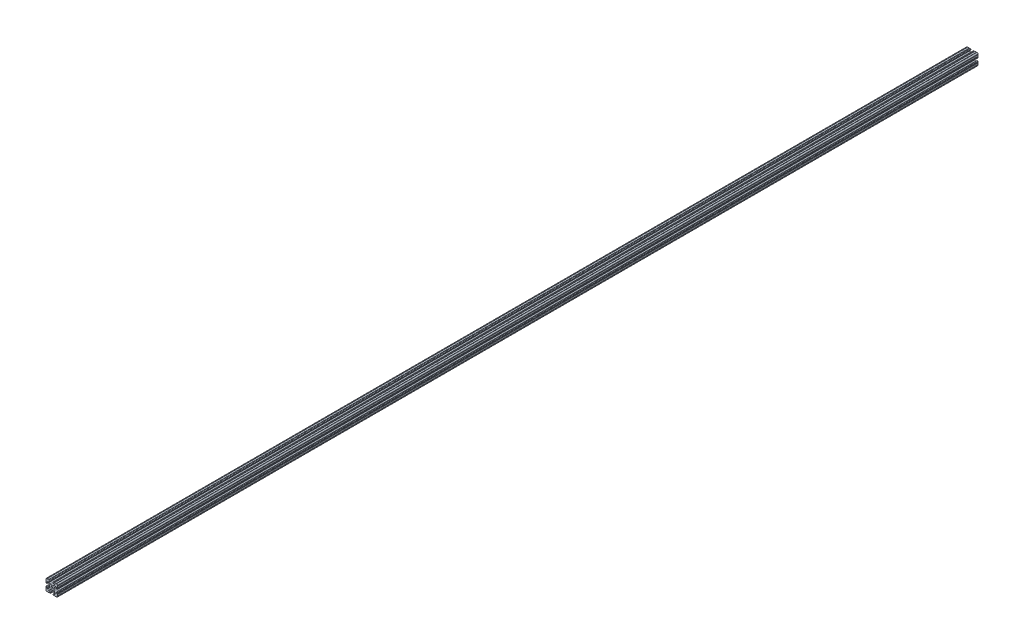
SolidWorks part; units mm, degrees
material "6061-T6 (SS)"
ref_plane "Front Plane" through (0, 0, 0) normal (0, 0, 1) x (1, 0, 0)
ref_plane "Top Plane" through (0, 0, 0) normal (0, 1, 0) x (1, 0, 0)
ref_plane "Right Plane" through (0, 0, 0) normal (1, 0, 0) x (0, 0, -1)
ref_plane "Plane1" through (0, 0, -304.8) normal (0, 0, -1) x (-1, 0, 0)
sketch "Sketch1" plane through (0, 0, -304.8) normal (0, 0, -1) x (-1, 0, 0)
  line L0 (14.3277, 19.05) -> (9.4982, 19.05)
  line L1 (7.9742, 19.05) -> (5.6176, 19.05)
  line L2 (4.064, 17.4964) -> (4.064, 16.5396)
  line L3 (5.6176, 14.986) -> (9.3853, 14.986)
  line L4 (10.287, 14.0843) -> (10.287, 13.5524)
  line L5 (10.0229, 12.9148) -> (5.2522, 8.144)
  line L6 (1.9022, 6.7564) -> (-1.9022, 6.7564)
  line L7 (-5.2522, 8.144) -> (-10.0229, 12.9148)
  line L8 (-10.287, 13.5524) -> (-10.287, 14.0843)
  line L9 (-9.3853, 14.986) -> (-5.6176, 14.986)
  line L10 (-4.064, 16.5396) -> (-4.064, 17.4964)
  line L11 (-5.6176, 19.05) -> (-7.9742, 19.05)
  line L12 (-9.4982, 19.05) -> (-14.3277, 19.05)
  line L13 (-19.05, 14.3277) -> (-19.05, 9.4961)
  line L14 (-19.05, 7.9763) -> (-19.05, 5.6176)
  line L15 (-17.4964, 4.064) -> (-16.5396, 4.064)
  line L16 (-14.986, 5.6176) -> (-14.986, 9.3853)
  line L17 (-14.0843, 10.287) -> (-13.516, 10.287)
  line L18 (-12.8784, 10.0229) -> (-8.1476, 5.2921)
  line L19 (-6.7564, 1.9335) -> (-6.7564, -1.9335)
  line L20 (-8.1476, -5.2921) -> (-12.8784, -10.0229)
  line L21 (-13.516, -10.287) -> (-14.0843, -10.287)
  line L22 (-14.986, -9.3853) -> (-14.986, -5.6176)
  line L23 (-16.5396, -4.064) -> (-17.4964, -4.064)
  line L24 (-19.05, -5.6176) -> (-19.05, -7.9763)
  line L25 (-19.05, -9.4961) -> (-19.05, -14.3277)
  line L26 (-14.3277, -19.05) -> (-9.4961, -19.05)
  line L27 (-7.9763, -19.05) -> (-5.6176, -19.05)
  line L28 (-4.064, -17.4964) -> (-4.064, -16.5396)
  line L29 (-5.6176, -14.986) -> (-9.3853, -14.986)
  line L30 (-10.287, -14.0843) -> (-10.287, -13.5524)
  line L31 (-10.0229, -12.9148) -> (-5.2522, -8.144)
  line L32 (-1.9022, -6.7564) -> (1.9022, -6.7564)
  line L33 (5.2522, -8.144) -> (10.0229, -12.9148)
  line L34 (10.287, -13.5524) -> (10.287, -14.0843)
  line L35 (9.3853, -14.986) -> (5.6176, -14.986)
  line L36 (4.064, -16.5396) -> (4.064, -17.4964)
  line L37 (5.6176, -19.05) -> (7.9763, -19.05)
  line L38 (9.4961, -19.05) -> (14.3277, -19.05)
  line L39 (19.05, -14.3277) -> (19.05, -9.4961)
  line L40 (19.05, -7.9763) -> (19.05, -5.6176)
  line L41 (17.4964, -4.064) -> (16.5396, -4.064)
  line L42 (14.986, -5.6176) -> (14.986, -9.3853)
  line L43 (14.0843, -10.287) -> (13.516, -10.287)
  line L44 (12.8784, -10.0229) -> (8.1476, -5.2921)
  line L45 (6.7564, -1.9335) -> (6.7564, 1.9335)
  line L46 (8.1476, 5.2921) -> (12.8784, 10.0229)
  line L47 (13.516, 10.287) -> (14.0843, 10.287)
  line L48 (14.986, 9.3853) -> (14.986, 5.6176)
  line L49 (16.5396, 4.064) -> (17.4964, 4.064)
  line L50 (19.05, 5.6176) -> (19.05, 7.9763)
  line L51 (19.05, 9.4961) -> (19.05, 14.3277)
  arc A0 (15.8475, 19.05) -> (14.3277, 19.05) centre (15.0876, 18.9933) cw
  arc A1 (9.4982, 19.05) -> (7.9742, 19.05) centre (8.7362, 19.05) cw
  arc A2 (5.6176, 19.05) -> (4.064, 17.4964) centre (5.6176, 17.4964) ccw
  arc A3 (4.064, 16.5396) -> (5.6176, 14.986) centre (5.6176, 16.5396) ccw
  arc A4 (9.3853, 14.986) -> (10.287, 14.0843) centre (9.3853, 14.0843) cw
  arc A5 (10.287, 13.5524) -> (10.0229, 12.9148) centre (9.3853, 13.5524) cw
  arc A6 (5.2522, 8.144) -> (1.9022, 6.7564) centre (1.9022, 11.494) cw
  arc A7 (-1.9022, 6.7564) -> (-5.2522, 8.144) centre (-1.9022, 11.494) cw
  arc A8 (-10.0229, 12.9148) -> (-10.287, 13.5524) centre (-9.3853, 13.5524) cw
  arc A9 (-10.287, 14.0843) -> (-9.3853, 14.986) centre (-9.3853, 14.0843) cw
  arc A10 (-5.6176, 14.986) -> (-4.064, 16.5396) centre (-5.6176, 16.5396) ccw
  arc A11 (-4.064, 17.4964) -> (-5.6176, 19.05) centre (-5.6176, 17.4964) ccw
  arc A12 (-7.9742, 19.05) -> (-9.4982, 19.05) centre (-8.7362, 19.05) cw
  arc A13 (-14.3277, 19.05) -> (-15.8475, 19.05) centre (-15.0876, 18.9933) cw
  arc A14 (-15.8475, 19.05) -> (-19.05, 15.8475) centre (-15.8751, 15.8751) ccw
  arc A15 (-19.05, 15.8475) -> (-19.05, 14.3277) centre (-18.9933, 15.0876) cw
  arc A16 (-19.05, 9.4961) -> (-19.05, 7.9763) centre (-18.9933, 8.7362) cw
  arc A17 (-19.05, 5.6176) -> (-17.4964, 4.064) centre (-17.4964, 5.6176) ccw
  arc A18 (-16.5396, 4.064) -> (-14.986, 5.6176) centre (-16.5396, 5.6176) ccw
  arc A19 (-14.986, 9.3853) -> (-14.0843, 10.287) centre (-14.0843, 9.3853) cw
  arc A20 (-13.516, 10.287) -> (-12.8784, 10.0229) centre (-13.516, 9.3853) cw
  arc A21 (-8.1476, 5.2921) -> (-6.7564, 1.9335) centre (-11.5062, 1.9335) cw
  arc A22 (-6.7564, -1.9335) -> (-8.1476, -5.2921) centre (-11.5062, -1.9335) cw
  arc A23 (-12.8784, -10.0229) -> (-13.516, -10.287) centre (-13.516, -9.3853) cw
  arc A24 (-14.0843, -10.287) -> (-14.986, -9.3853) centre (-14.0843, -9.3853) cw
  arc A25 (-14.986, -5.6176) -> (-16.5396, -4.064) centre (-16.5396, -5.6176) ccw
  arc A26 (-17.4964, -4.064) -> (-19.05, -5.6176) centre (-17.4964, -5.6176) ccw
  arc A27 (-19.05, -7.9763) -> (-19.05, -9.4961) centre (-18.9933, -8.7362) cw
  arc A28 (-19.05, -14.3277) -> (-19.05, -15.8475) centre (-18.9933, -15.0876) cw
  arc A29 (-19.05, -15.8475) -> (-15.8475, -19.05) centre (-15.8751, -15.8751) ccw
  arc A30 (-15.8475, -19.05) -> (-14.3277, -19.05) centre (-15.0876, -18.9933) cw
  arc A31 (-9.4961, -19.05) -> (-7.9763, -19.05) centre (-8.7362, -18.9933) cw
  arc A32 (-5.6176, -19.05) -> (-4.064, -17.4964) centre (-5.6176, -17.4964) ccw
  arc A33 (-4.064, -16.5396) -> (-5.6176, -14.986) centre (-5.6176, -16.5396) ccw
  arc A34 (-9.3853, -14.986) -> (-10.287, -14.0843) centre (-9.3853, -14.0843) cw
  arc A35 (-10.287, -13.5524) -> (-10.0229, -12.9148) centre (-9.3853, -13.5524) cw
  arc A36 (-5.2522, -8.144) -> (-1.9022, -6.7564) centre (-1.9022, -11.494) cw
  arc A37 (1.9022, -6.7564) -> (5.2522, -8.144) centre (1.9022, -11.494) cw
  arc A38 (10.0229, -12.9148) -> (10.287, -13.5524) centre (9.3853, -13.5524) cw
  arc A39 (10.287, -14.0843) -> (9.3853, -14.986) centre (9.3853, -14.0843) cw
  arc A40 (5.6176, -14.986) -> (4.064, -16.5396) centre (5.6176, -16.5396) ccw
  arc A41 (4.064, -17.4964) -> (5.6176, -19.05) centre (5.6176, -17.4964) ccw
  arc A42 (7.9763, -19.05) -> (9.4961, -19.05) centre (8.7362, -18.9933) cw
  arc A43 (14.3277, -19.05) -> (15.8475, -19.05) centre (15.0876, -18.9933) cw
  arc A44 (15.8475, -19.05) -> (19.05, -15.8475) centre (15.8751, -15.8751) ccw
  arc A45 (19.05, -15.8475) -> (19.05, -14.3277) centre (18.9933, -15.0876) cw
  arc A46 (19.05, -9.4961) -> (19.05, -7.9763) centre (18.9933, -8.7362) cw
  arc A47 (19.05, -5.6176) -> (17.4964, -4.064) centre (17.4964, -5.6176) ccw
  arc A48 (16.5396, -4.064) -> (14.986, -5.6176) centre (16.5396, -5.6176) ccw
  arc A49 (14.986, -9.3853) -> (14.0843, -10.287) centre (14.0843, -9.3853) cw
  arc A50 (13.516, -10.287) -> (12.8784, -10.0229) centre (13.516, -9.3853) cw
  arc A51 (8.1476, -5.2921) -> (6.7564, -1.9335) centre (11.5062, -1.9335) cw
  arc A52 (6.7564, 1.9335) -> (8.1476, 5.2921) centre (11.5062, 1.9335) cw
  arc A53 (12.8784, 10.0229) -> (13.516, 10.287) centre (13.516, 9.3853) cw
  arc A54 (14.0843, 10.287) -> (14.986, 9.3853) centre (14.0843, 9.3853) cw
  arc A55 (14.986, 5.6176) -> (16.5396, 4.064) centre (16.5396, 5.6176) ccw
  arc A56 (17.4964, 4.064) -> (19.05, 5.6176) centre (17.4964, 5.6176) ccw
  arc A57 (19.05, 7.9763) -> (19.05, 9.4961) centre (18.9933, 8.7362) cw
  arc A58 (19.05, 14.3277) -> (19.05, 15.8475) centre (18.9933, 15.0876) cw
  arc A59 (19.05, 15.8475) -> (15.8475, 19.05) centre (15.8751, 15.8751) ccw
  circle A60 centre (0, 0) radius 3.3274
extrude "Boss-Extrude1" add sketch "Sketch1" against normal blind 3048
